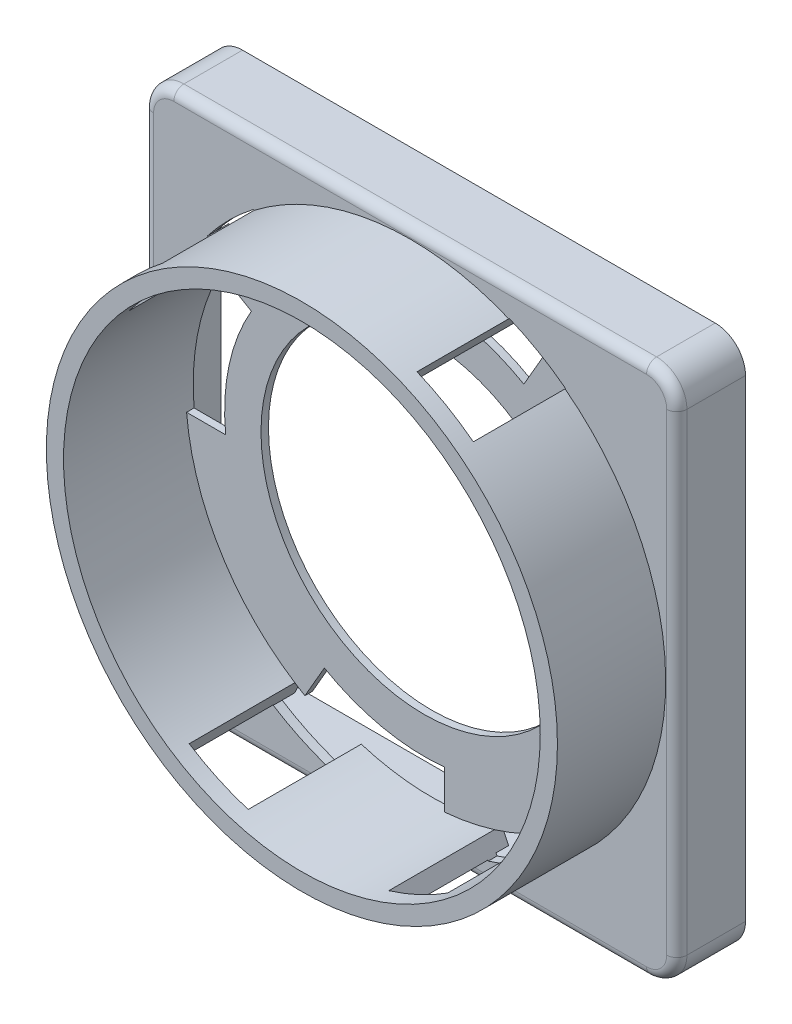
SolidWorks part; units mm, degrees
ref_plane "Front" through (0, 0, 0) normal (0, 0, 1) x (1, 0, 0)
ref_plane "Top" through (0, 0, 0) normal (0, 1, 0) x (1, 0, 0)
ref_plane "Right" through (0, 0, 0) normal (1, 0, 0) x (0, 0, -1)
sketch "Sketch1" plane through (0, 0, 0) normal (0, 0, 1) x (1, 0, 0)
  line L1 (3.81, 0) -> (63.246, 0)
  line L2 (0, 3.81) -> (0, 63.246)
  line L3 (3.81, 67.056) -> (63.246, 67.056)
  line L4 (67.056, 3.81) -> (67.056, 63.246)
  arc A0 (0, 3.81) -> (3.81, 0) centre (3.81, 3.81) ccw
  arc A1 (3.81, 67.056) -> (0, 63.246) centre (3.81, 63.246) ccw
  arc A2 (67.056, 63.246) -> (63.246, 67.056) centre (63.246, 63.246) ccw
  arc A3 (67.056, 3.81) -> (63.246, 0) centre (63.246, 3.81) cw
  point P7 (0, 0)
  point P10 (0, 67.056)
  point P13 (67.056, 67.056)
  point P16 (67.056, 0)
  dimension "D3" = 3.81
  dimension "D1" = 67.056
  dimension "D2" = 67.056
extrude "Base-Extrude" add sketch "Sketch1" against normal blind 8.636
shell "Shell1" thickness 1.1176
sketch "Sketch2" plane through (0, 0, 0) normal (0, 0, 1) x (1, 0, 0)
  line L0 (0, 63.246) -> (0, 3.81) construction
  line L1 (63.246, 67.056) -> (3.81, 67.056) construction
  circle A0 centre (33.528, 33.528) radius 32.131
  dimension "D1" = 64.262
  dimension "D2" = 33.528
  dimension "D3" = 33.528
extrude "Boss-Extrude1" add sketch "Sketch2" along normal blind 13.6144
sketch "Sketch3" plane through (0, 0, -1.1176) normal (0, 0, -1) x (-1, 0, 0)
  circle A0 centre (-33.528, 33.528) radius 32.2326
  dimension "D1" = 64.4652
extrude "Boss-Extrude2" add sketch "Sketch3" along normal blind 1.5748
sketch "Sketch4" plane through (0, 0, -2.6924) normal (0, 0, -1) x (-1, 0, 0)
  line L8 (-3.81, 63.9572) -> (-63.246, 63.9572)
  line L9 (-3.0988, 3.81) -> (-3.0988, 63.246)
  line L10 (-63.246, 3.0988) -> (-3.81, 3.0988)
  line L11 (-63.9572, 63.246) -> (-63.9572, 3.81)
  line L12 (-3.81, 63.9572) -> (-63.246, 63.9572)
  line L13 (-3.0988, 3.81) -> (-3.0988, 63.246)
  line L14 (-63.246, 3.0988) -> (-3.81, 3.0988)
  line L15 (-63.9572, 63.246) -> (-63.9572, 3.81)
  line L16 (-63.246, 65.9384) -> (-3.81, 65.9384) construction
  line L17 (-1.1176, 63.246) -> (-1.1176, 3.81) construction
  line L18 (-3.81, 1.1176) -> (-63.246, 1.1176) construction
  line L19 (-65.9384, 3.81) -> (-65.9384, 63.246) construction
  line L20 (-63.246, 65.9384) -> (-3.81, 65.9384)
  line L21 (-1.1176, 63.246) -> (-1.1176, 3.81)
  line L22 (-3.81, 1.1176) -> (-63.246, 1.1176)
  line L23 (-65.9384, 3.81) -> (-65.9384, 63.246)
  arc A8 (-63.246, 63.9572) -> (-63.9572, 63.246) centre (-63.246, 63.246) ccw
  arc A9 (-3.0988, 63.246) -> (-3.81, 63.9572) centre (-3.81, 63.246) ccw
  arc A10 (-3.81, 3.0988) -> (-3.0988, 3.81) centre (-3.81, 3.81) ccw
  arc A11 (-63.9572, 3.81) -> (-63.246, 3.0988) centre (-63.246, 3.81) ccw
  arc A12 (-63.246, 63.9572) -> (-63.9572, 63.246) centre (-63.246, 63.246) ccw
  arc A13 (-3.0988, 63.246) -> (-3.81, 63.9572) centre (-3.81, 63.246) ccw
  arc A14 (-3.81, 3.0988) -> (-3.0988, 3.81) centre (-3.81, 3.81) ccw
  arc A15 (-63.9572, 3.81) -> (-63.246, 3.0988) centre (-63.246, 3.81) ccw
  arc A16 (-63.246, 65.9384) -> (-65.9384, 63.246) centre (-63.246, 63.246) ccw construction
  arc A17 (-1.1176, 63.246) -> (-3.81, 65.9384) centre (-3.81, 63.246) ccw construction
  arc A18 (-3.81, 1.1176) -> (-1.1176, 3.81) centre (-3.81, 3.81) ccw construction
  arc A19 (-65.9384, 3.81) -> (-63.246, 1.1176) centre (-63.246, 3.81) ccw construction
  arc A20 (-63.246, 65.9384) -> (-65.9384, 63.246) centre (-63.246, 63.246) ccw
  arc A21 (-1.1176, 63.246) -> (-3.81, 65.9384) centre (-3.81, 63.246) ccw
  arc A22 (-3.81, 1.1176) -> (-1.1176, 3.81) centre (-3.81, 3.81) ccw
  arc A23 (-65.9384, 3.81) -> (-63.246, 1.1176) centre (-63.246, 3.81) ccw
  dimension "D1" = 1.9812
extrude "Cut-Extrude2" cut sketch "Sketch4" against normal up to surface (1.5748 mm away)
sketch "Sketch5" plane through (0, 0, 13.6144) normal (0, 0, 1) x (1, 0, 0)
  circle A1 centre (33.528, 33.528) radius 29.972
  dimension "D1" = 59.944
extrude "Cut-Extrude3" cut sketch "Sketch5" against normal blind 15.367
sketch "Sketch6" plane through (0, 0, -1.7526) normal (0, 0, 1) x (1, 0, 0)
  circle A0 centre (33.528, 33.528) radius 20.5105
  dimension "D1" = 41.021
extrude "Cut-Extrude4" cut sketch "Sketch6" against normal through all
sketch "Sketch7" plane through (0, 0, -1.7526) normal (0, 0, 1) x (1, 0, 0)
  line L0 (30.988, 63.3922) -> (30.988, 58.4816)
  line L1 (46.0692, 55.2501) -> (48.514, 59.4845)
  line L2 (33.528, 33.528) -> (48.514, 59.4845) construction
  line L3 (33.528, 70.0698) -> (33.528, -3.1098) construction
  circle A0 centre (33.528, 33.528) radius 29.972 construction
  circle A2 centre (33.528, 33.528) radius 20.5105 construction
  arc A3 (46.0692, 55.2501) -> (30.988, 58.4816) centre (33.528, 33.528) ccw
  arc A4 (48.514, 59.4845) -> (30.988, 63.3922) centre (33.528, 33.528) ccw
  dimension "D2" = 50.165
  dimension "D1" = 2.54
  dimension "D3" = 30
extrude "Cut-Extrude5" cut sketch "Sketch7" against normal through all
pattern_circular "CirPattern1" count 4 over 360 about axis through (33.528, 33.528, 0) along (0, 0, 1) of "Cut-Extrude5"
sketch "Sketch8" plane through (0, 0, -2.6924) normal (0, 0, -1) x (-1, 0, 0)
  line L0 (-33.528, 33.528) -> (-48.514, 59.4845) construction
  line L1 (-45.9725, 63.2614) -> (-44.8323, 61.2865)
  line L2 (-53.0556, 59.172) -> (-51.9154, 57.1971)
  circle A1 centre (-33.528, 33.528) radius 29.972 construction
  arc A3 (-44.8323, 61.2865) -> (-51.9154, 57.1971) centre (-33.528, 33.528) ccw
  arc A4 (-44.1583, 63.9572) -> (-63.9572, 44.1583) centre (-33.528, 33.528) ccw construction
  arc A5 (-45.9725, 63.2614) -> (-53.0556, 59.172) centre (-33.528, 33.528) ccw
  dimension "D1" = 4.0894
  dimension "D2" = 8.1788
extrude "Cut-Extrude6" cut sketch "Sketch8" against normal blind 14.224
sketch "Sketch9" plane through (0, 0, -2.6924) normal (0, 0, -1) x (-1, 0, 0)
  line L0 (-33.528, 33.528) -> (-10.808, 56.248) construction
  line L1 (-3.6638, 30.988) -> (-8.5744, 30.988) construction
  line L2 (-8.0286, 53.2441) -> (-9.6411, 51.6316)
  line L3 (-13.8119, 59.0274) -> (-15.4244, 57.4149)
  circle A0 centre (-33.528, 33.528) radius 32.131 construction
  circle A1 centre (-33.528, 33.528) radius 29.972 construction
  arc A2 (-9.6411, 51.6316) -> (-15.4244, 57.4149) centre (-33.528, 33.528) ccw
  arc A3 (-3.0988, 44.1583) -> (-22.8977, 63.9572) centre (-33.528, 33.528) ccw construction
  arc A4 (-8.0286, 53.2441) -> (-13.8119, 59.0274) centre (-33.528, 33.528) ccw
  dimension "D1" = 45
  dimension "D2" = 4.0894
  dimension "D3" = 8.1788
extrude "Cut-Extrude7" cut sketch "Sketch9" against normal blind 14.224
sketch "Sketch10" plane through (0, 0, -2.6924) normal (0, 0, -1) x (-1, 0, 0)
  line L0 (-33.528, 33.528) -> (-19.9489, 4.4074) construction
  line L1 (-36.068, 3.6638) -> (-36.068, 8.5744) construction
  line L2 (-17.2735, 8.3464) -> (-16.3097, 6.2797)
  line L3 (-24.686, 4.8899) -> (-23.8508, 3.0988)
  line L4 (-44.1583, 3.0988) -> (-22.8977, 3.0988) construction
  line L5 (-23.8508, 3.0988) -> (-22.8977, 3.0988)
  circle A0 centre (-33.528, 33.528) radius 32.131 construction
  circle A1 centre (-33.528, 33.528) radius 29.972 construction
  arc A2 (-22.8977, 3.0988) -> (-3.0988, 22.8977) centre (-33.528, 33.528) ccw construction
  arc A3 (-24.686, 4.8899) -> (-17.2735, 8.3464) centre (-33.528, 33.528) ccw
  arc A4 (-22.8977, 3.0988) -> (-16.3097, 6.2797) centre (-33.528, 33.528) ccw
  dimension "D1" = 25
  dimension "D2" = 4.0894
  dimension "D3" = 8.1788
extrude "Cut-Extrude8" cut sketch "Sketch10" against normal blind 14.224
pattern_circular "CirPattern2" count 2 over 310 about axis through (33.528, 33.528, 0) along (0, 0, 1) of "Cut-Extrude8"
fillet "Fillet1" radius 1.27 8 edges at (65.9401, 65.9401, 0) (67.056, 33.528, 0) (65.9401, 1.1159, 0) (33.528, 0, 0) (1.1159, 1.1159, 0) (0, 33.528, 0) (1.1159, 65.9401, 0) (33.528, 67.056, 0)
